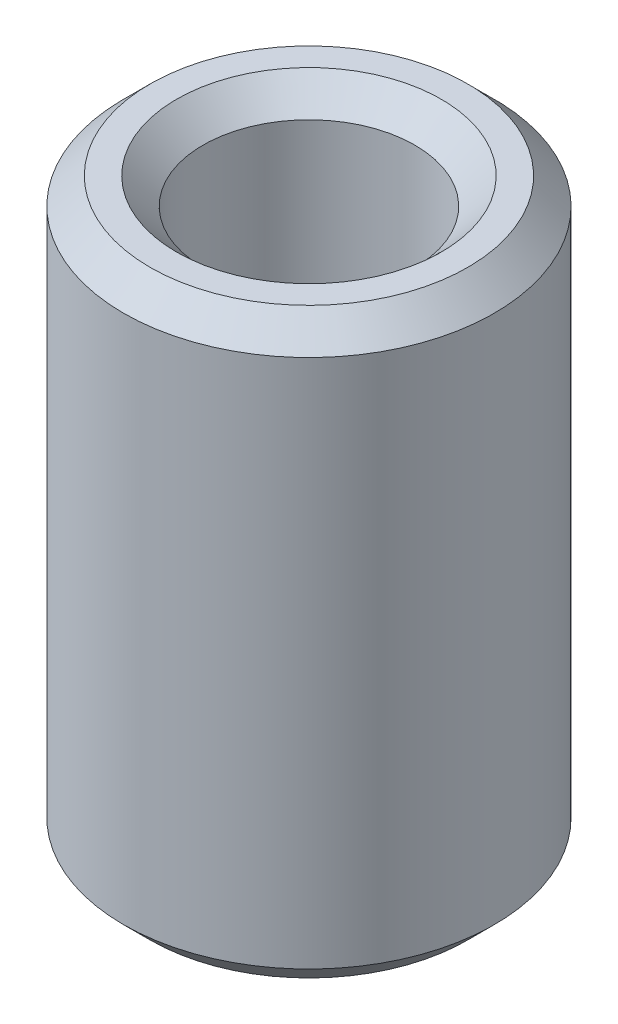
SolidWorks part; units mm, degrees
ref_plane "Front Plane" through (0, 0, 0) normal (0, 0, 1) x (1, 0, 0)
ref_plane "Top Plane" through (0, 0, 0) normal (0, 1, 0) x (1, 0, 0)
ref_plane "Right Plane" through (0, 0, 0) normal (1, 0, 0) x (0, 0, -1)
sketch "Sketch1" plane through (0, 0, 0) normal (0, 1, 0) x (1, 0, 0)
  circle A0 centre (0, 0) radius 4
  circle A1 centre (0, 0) radius 7
  dimension "D1" = 8
  dimension "D2" = 14
extrude "Boss-Extrude1" add sketch "Sketch1" along normal blind 22
chamfer "Chamfer1" distance 1 angle 45 4 edges at (0, 0, 4) (0, 0, 7) (0, 22, 7) (0, 22, 4)
